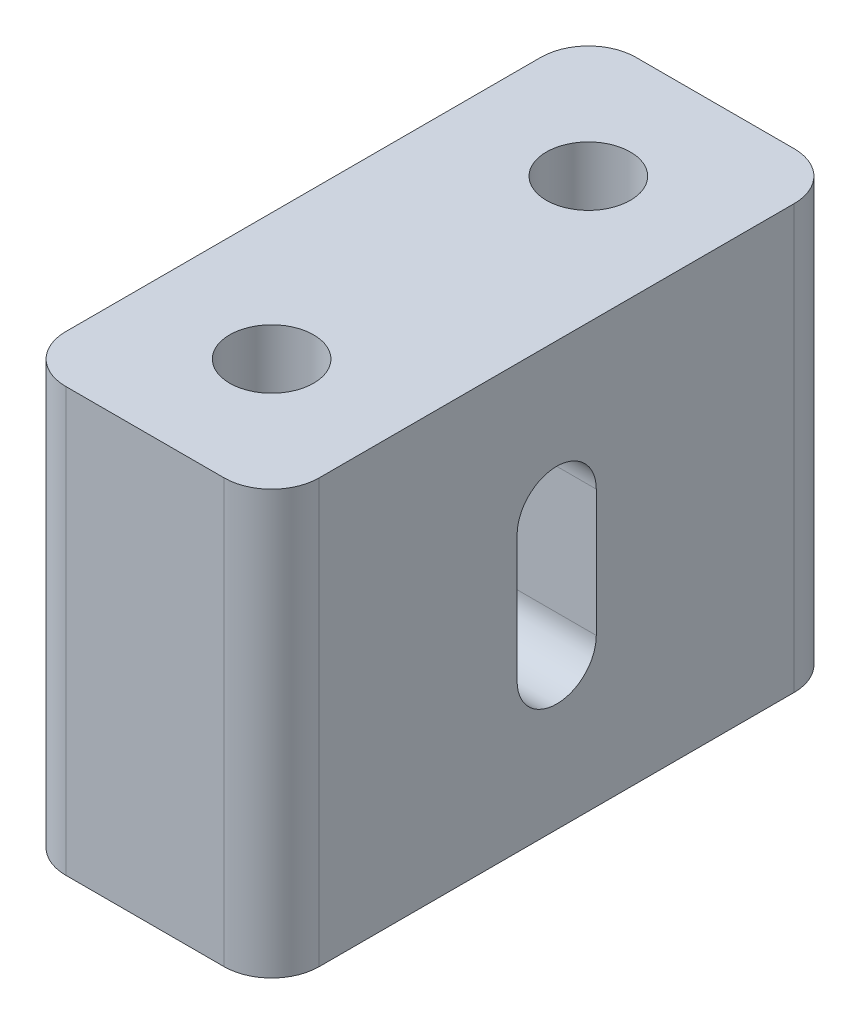
SolidWorks part; units mm, degrees
material "ABS"
ref_plane "Front Plane" through (0, 0, 0) normal (0, 0, 1) x (1, 0, 0)
ref_plane "Top Plane" through (0, 0, 0) normal (0, 1, 0) x (1, 0, 0)
ref_plane "Right Plane" through (0, 0, 0) normal (1, 0, 0) x (0, 0, -1)
sketch "Sketch1" plane through (0, 0, 0) normal (0, 1, 0) x (1, 0, 0)
  line L0 (-8, 5) -> (8, 5) construction
  line L1 (-8, -18) -> (8, -18)
  line L2 (-8, -18) -> (-8, 18)
  line L3 (-8, 18) -> (8, 18)
  line L4 (8, -18) -> (8, 18)
  line L5 (-8, -18) -> (8, 18) construction
  line L6 (-8, 18) -> (8, -18) construction
  line L7 (8, -5) -> (-8, -5) construction
  line L8 (-8, -5) -> (8, 5) construction
  circle A0 centre (0, 10) radius 5 construction
  circle A1 centre (0, -10) radius 5 construction
  circle A2 centre (0, 10) radius 8 construction
  point P0 (0, 0)
  point P12 (0, 0)
  dimension "D2" = 10
  dimension "D1" = 10
  dimension "D3" = 3
extrude "Boss-Extrude1" add sketch "Sketch1" along normal mid plane 26.7324 contours L3 L4 L1 L2
hole_wizard "M5 Clearance Hole1" positions "Sketch2" profile "Sketch3" hole size "M5" standard "ANSI Metric" end condition through all
sketch "Sketch2" plane through (0, 13.3662, 0) normal (0, 1, 0) x (1, 0, 0)
  point P0 (0, 10)
  point P3 (0, -10)
sketch "Sketch3" plane through (0, 13.3662, -10) normal (1, 0, 0) x (0, 0, 1)
  line L0 (0, 0) -> (0, 26.7324)
  line L1 (0, 26.7324) -> (2.65, 26.7324)
  line L2 (2.65, 26.7324) -> (2.65, 0)
  line L5 (2.65, 0) -> (0, 0)
  line L11 (0, -6.35) -> (0, 107.95) construction
  dimension "Thru Hole Dia." = 5.3
  dimension "Thru Hole Depth" = 26.7324
fillet "Fillet1" radius 3 4 edges at (-8, 0, -18) (8, 0, -18) (-8, 0, 18) (8, 0, 18)
sketch "Sketch6" plane through (0, 0, 0) normal (1, 0, 0) x (0, 0, -1)
  line L0 (0, -4) -> (0, 4) construction
  line L1 (-2.5, -4) -> (-2.5, 4)
  line L2 (2.5, -4) -> (2.5, 4)
  arc A0 (-2.5, -4) -> (2.5, -4) centre (0, -4) ccw
  arc A1 (2.5, 4) -> (-2.5, 4) centre (0, 4) ccw
  point P2 (0, 0)
  dimension "D1" = 2.5
  dimension "D2" = 8
extrude "Cut-Extrude1" cut sketch "Sketch6" against normal through all both and the other way through all
equation "\"ExtrusionStandard\"= 20mm'Size of extrusion used for framing"
equation "\"BaseExtrusionFrameWidth\"= 60mm'Width of the central aluminum extrusion"
equation "\"BaseExtrusionFrameHeight\"= 20mm'Height of the central aluminum extrusion"
equation "\"PlateThickness\"= 15mm'Thickness of the the front and back framing plates"
equation "\"RailHeight\"= 13mm'Total height of the carriage and rail component"
equation "\"WallThickness\"= 3mm'Standard wall thickness"
equation "\"ShaftDiameter\"= 20mm'Outside Diameter of the main yoke shaft"
equation "\"ShaftClearance\"= 1mm'Clearance/gap between the main yoke and non-bearing elements"
equation "\"PlainBearingBoltCircleDiameter\"= ( \"WallThickness\" + \"M3_ClearanceDiameter\" / 2 ) * 2 + \"PlainBearingOD\"'Bolt circle diameter for the plain bearing retainer/mount"
equation "\"PlainBearingBoltcount\"= 5'Number of bolts used in the plain bearing/mount"
equation "\"X_ThrustBearingOD\"= 35mm'OD of the thrust bearing used on the main shaft"
equation "\"X_ThrustBearingID\"= 20mm'ID of the thrust bearing used on the main shaft"
equation "\"X_ThrustBearingThickness\"= 10mm'Thickness of the thrust bearing used on the main shaft"
equation "\"X_RearCollarOD\"= 32mm'OD of the shaft collar of the main shaft"
equation "\"X_RearCollarID\"= 20mm'ID of the shaft collar of the main shaft"
equation "\"X_RearCollarThickness\"= 8mm'Thickness of the collar along the main shaft"
equation "\"LeadScrewDiameter\"= 6.35mm'OD of the leadsrew used on the Y axis"
equation "\"LeadScrewHeight\"= 10mm'Height of the center of the Lead screw from bottom of gantry extrusion"
equation "\"LeadScrewNut_FlangeOD\"= 25mm'OD of the lead screw nut flange"
equation "\"LeadScrewNut_BoltCircleDiameter\"= 19mm'Bolt circle diameter needed to mount the leadscrew nut"
equation "\"LeadScrewNut_BoltCount\"= 6'Number of bolts required to mount the leadscrew nut to gantry."
equation "\"Pillow_BaseClearance\"= 6mm + \"WallThickness\"'Pillow block base needed to internally mount screws"
equation "\"X_PillowHeight\"= \"Pillow_BaseClearance\" + \"calc_X_PillowRadius\"'Height of the main shaft pillow block base, as measured from the top of the gantry surface"
equation "\"X_BeltPitch\"= 2mm'Pitch of the timing belt used on the X axis/main shaft."
equation "\"X_Drive_Teeth\"= 20'Number of teeth used on the X/Main stepper motor pulley"
equation "\"X_Shaft_Teeth\"= 60'Number of teeth on the X/Main shaft pulley"
equation "\"X_Drive_PD\"= ( \"X_Drive_Teeth\" * \"X_BeltPitch\" ) / PI'Pitch Diameter of the X/main motor pulley"
equation "\"X_Shaft_PD\"= ( \"X_Shaft_Teeth\" * \"X_BeltPitch\" ) / PI'Pitch Diameter of the X/main shaft pulley"
equation "\"X_CenterDistance\" = 60mm'Distance between the main shaft and motor pulley centers"
equation "\"GantryLength\"= 150mm'Length of the gantry extrusion/plate"
equation "\"X_MotorPlateThickness\"= 15mm'Thickness of the plate used to hold the X/main motor"
equation "\"X_MotorPlateLength\"= \"X_MotorPlateThickness\" + \"ExtrusionStandard\" * 2'FIXME"
equation "\"X_BeltWidth\" = 9mm'Width of the timing belt used on the X/Main shaft rotary drive"
equation "\"X_PillowLength\"= ( \"WallThickness\" * 4 ) + \"X_RearCollarThickness\" + ( \"X_ThrustBearingThickness\" * 2 ) + \"X_ShaftRotaryBearingThickness\"'Total length of the pillow block used to hold the main shaft"
equation "\"X_ShaftRotaryBearingThickness\"= 9mm'Thickness of the radial bearing used on the main shaft"
equation "\"X_ShaftRotaryBearingOD\"= 37mm'OD of the radial bearing used on the main shaft"
equation "\"ShaftLength\"= 400mm'Length of the main shaft."
equation "\"PlainBearingOD\"= 31.8mm'OD of the Plain Bearing housing"
equation "\"Y_Drive_Length\"= \"ShaftLength\"'duplicate"
equation "\"Y_Drive_Diameter\"= \"LeadScrewDiameter\"'duplicate"
equation "\"Y_Drive_ThrustBearingOD\"= .5625in'OD of the thrust bearings used to support the leadscrew/Y drive"
equation "\"Y_Drive_ThrustBearingThickness\"= .193in'Thickness of the thrust bearings used to support the leadscrew/Y drive"
equation "\"Y_Drive_ShaftCollarOD\"= .6875in'OD of the collar used to constrain the leadscrew/Y drive"
equation "\"Y_Drive_ShaftCollarThickness\"= .3125in'Thickness of the collar used to constrain the leadscrew/Y drive"
equation "\"Y_Drive_ShaftCollarClearance\"= .375in / 2'Amount of radial clearance needed around the leadscrew/Y shaft collar"
equation "\"calc_Y_Drive_BearingLargestDiameter\"= IIF ( \"Y_Drive_ThrustBearingOD\" > \"Y_Drive_ShaftCollarOD\" , \"Y_Drive_ThrustBearingOD\" , \"Y_Drive_ShaftCollarOD\" )'FIXME - calculated diameter needed for Y drive pillow - needs to account for collar clearance."
equation "\"Y_Drive_BearingBoltCircleDiameter\"= \"calc_Y_Drive_BearingLargestDiameter\" + ( \"Y_Drive_ShaftCollarClearance\" * 2 ) + ( \"WallThickness\" * 2 ) + 2 * 10mm'FIXME - unused?"
equation "\"M3_ClearanceDiameter\"= 8mm'Keepout diameter for M3 holes"
equation "\"M5_ClearanceDiameter\"= 10mm'Keepout Diameter for M5 holes"
equation "\"Y_Drive_CenterDistance\"= 65mm'Center Distance between Y motor drive and leadscrew pulley"
equation "\"Y_Drive_Teeth\"= 20'Number of teeth on the Y/linear stepper pulley"
equation "\"Y_Drive_ShaftTeeth\"= 60'Number of teeth on the Y/linear leadscrew pulley"
equation "\"Y_Drive_BeltWidth\"= 9mm'Width of the belt used on the Y/linear drive"
equation "\"Y_Drive_BeltPitch\"= 2mm'Pitch of the timing belt used on the Y/linear drive"
equation "\"Y_Drive_PD\"= ( \"Y_Drive_Teeth\" * \"Y_Drive_BeltPitch\" ) / PI'Pitch Diameter of the stepper pulley for the Y/linear drive"
equation "\"Y_Drive_ShaftPD\"= ( \"Y_Drive_ShaftTeeth\" * \"Y_Drive_BeltPitch\" ) / PI'Pitch diameter of the pulley on the Y/linear leadscrew"
equation "\"PlainBearingLength\"= 44.8mm'Length of the plain bearing housing"
equation "\"Y_Drive_ShaftBearingThickness\"= .196in'Thickness of the radial bearing used to support the Y leadscrew"
equation "\"Y_Drive_ShaftBearingOD\"= .625in'OD of the radial bearing used to support the Y leadscrew"
equation "\"EncoderMount_BoltWidth\"= 80mm"
equation "\"EncoderMount_BoltRowCount\" = 1"
equation "\"EncoderMount_BoltRowDistance\"= 20mm"
equation "\"EncoderMount_Offset\"= 10mm"
equation "\"Y_Drive_StepperShaftLength\"= 21mm"
equation "\"X_StepperShaftLength\" = 21mm"
equation "\"Y_DriveStepperShaftDiameter\"= 6.35mm"
equation "\"X_StepperShaftDiameter\"= 6.35mm"
equation "\"calc_X_PillowRadius\"= IIF ( ( \"X_ThrustBearingOD\" / 2 ) > ( \"X_RearCollarOD\" / 2 * 1.5 ) , \"X_ThrustBearingOD\" / 2 , ( \"X_RearCollarOD\" / 2 ) * 1.5 ) + ( \"WallThickness\" )'Minimum Radius needed for X/main shaft pillow block elements."
equation "\"calc_Y_PillowRadius\"= IIF ( \"Y_Drive_ThrustBearingOD\" / 2 > ( \"Y_Drive_ShaftCollarOD\" / 2 * 1.5 ) , \"Y_Drive_ThrustBearingOD\" / 2 , ( \"Y_Drive_ShaftCollarOD\" / 2 ) * 1.5 )'Minimum radius needed for the Y/linear shaft pillow block elements"
equation "\"Y_PillowHeight\"= \"Pillow_BaseClearance\" + \"calc_Y_PillowRadius\"'Height of the Y/linear pillow block base"
equation "\"Assembly_MainShaftStickout\"= 50mm'Amount of stickout at maximum pitch down (yoke forward)"
equation "\"GantryHeight\"= \"ExtrusionStandard\"'Height of the Gantry, including carriage mounting brackets"
equation "\"Y_StepperFrameSize\"= 57mm"
equation "\"Y_StepperHoleMountingDistance\"= 47mm"
equation "\"SidePanelHeight\" = \"Y_StepperFrameSize\" / 2 + \"X_CenterDistance\" + \"X_PillowHeight\" + \"GantryHeight\" + \"RailHeight\" + \"ExtrusionStandard\" - ( \"ExtrusionStandard\" * 3 ) + \"TopClearance\""
equation "\"TopClearance\"= 5mm"
equation "\"ExtrusionLength\"= 400mm"
equation "\"TopPanelWidth\" = 150mm"
equation "\"BodyPanelThickness\"= .25in'Thickness of side and top body panels."
equation "\"D1@Sketch1\"=\"M5_ClearanceDiameter\""
equation "\"D2@Sketch1\"=\"M5_ClearanceDiameter\""
equation "\"D3@Sketch1\"=\"WallThickness\""
equation "\"D1@Boss-Extrude1\"=\"X_Drive_PD\"+\"WallThickness\"*2+\"M3_ClearanceDiameter\""
equation "\"D1@Fillet1\"=\"WallThickness\""
equation "\"D1@Sketch6\"=5mm/2"
equation "\"D2@Sketch6\"=\"M3_ClearanceDiameter\""
